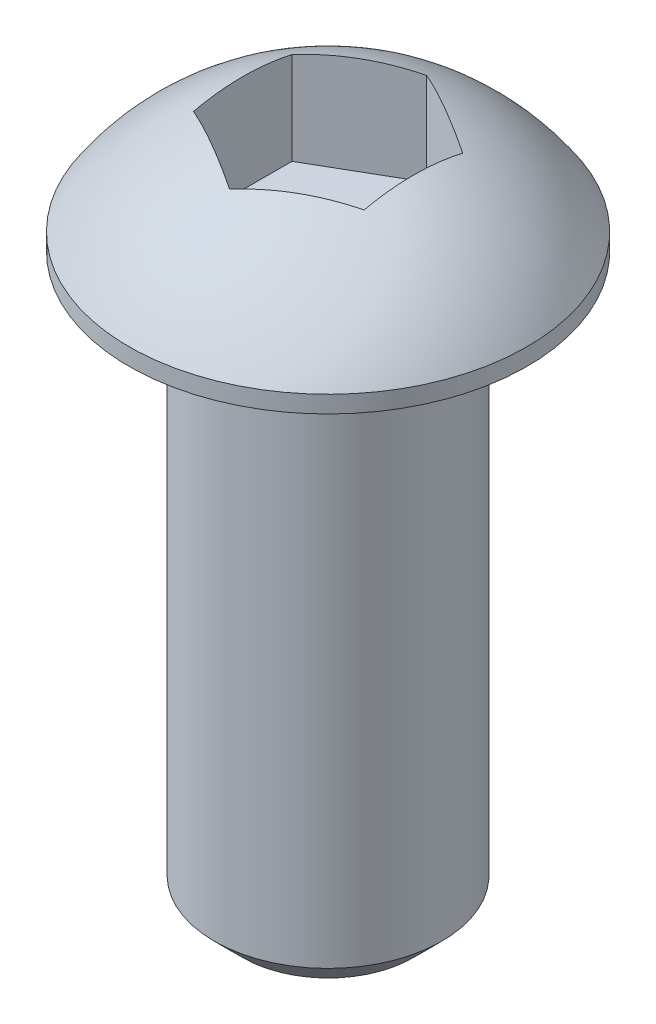
SolidWorks part; units mm, degrees
material "1.6523 (20NiCrMoS2-2)"
ref_plane "Front Plane" through (0, 0, 0) normal (0, 0, 1) x (1, 0, 0)
ref_plane "Top Plane" through (0, 0, 0) normal (0, 1, 0) x (1, 0, 0)
ref_plane "Right Plane" through (0, 0, 0) normal (1, 0, 0) x (0, 0, -1)
sketch "Sketch1" plane through (0, 0, 0) normal (0, 1, 0) x (1, 0, 0)
  circle A0 centre (0, 0) radius 2
  circle A1 centre (0, 0) radius 3.5
  dimension "D1" = 4
  dimension "D2" = 7
extrude "Boss-Extrude3" add sketch "Sketch1" against normal blind 10 contours A0
sketch "Sketch3" plane through (0, 0, 0) normal (0, 0, 1) x (1, 0, 0)
  line L0 (-3.5, 0) -> (-3.5, 0.3)
  line L1 (3.5, 0) -> (-3.5, 0) construction
  line L4 (0, -2) -> (0, 2.3599) construction
  line L5 (-3.5, 0) -> (0, 0)
  line L6 (0, 2.1881) -> (0, 0)
  arc A0 (-3.5, 0.3) -> (0, 2.1881) centre (0, -2) cw
  dimension "D1" = 7
  dimension "D2" = 0.3
  dimension "D3" = 2
revolve "Revolve2" add sketch "Sketch3" angle 360 about L4
chamfer "Chamfer2" distance 0.5 angle 45 1 edges at (0, -10, 2)
ref_plane "Plane1" through (0, 2.1881, 0) normal (0, 1, 0) x (1, 0, 0)
sketch "Sketch4" plane through (0, 2.1881, 0) normal (0, 1, 0) x (1, 0, 0)
  line L1 (0, 1.7321) -> (-1.5, 0.866)
  line L2 (-1.5, 0.866) -> (-1.5, -0.866)
  line L3 (-1.5, -0.866) -> (0, -1.7321)
  line L4 (0, -1.7321) -> (1.5, -0.866)
  line L5 (1.5, -0.866) -> (1.5, 0.866)
  line L6 (1.5, 0.866) -> (0, 1.7321)
  circle A0 centre (0, 0) radius 1.5 construction
  dimension "D1" = 3
extrude "Cut-Extrude2" cut sketch "Sketch4" against normal blind 2
